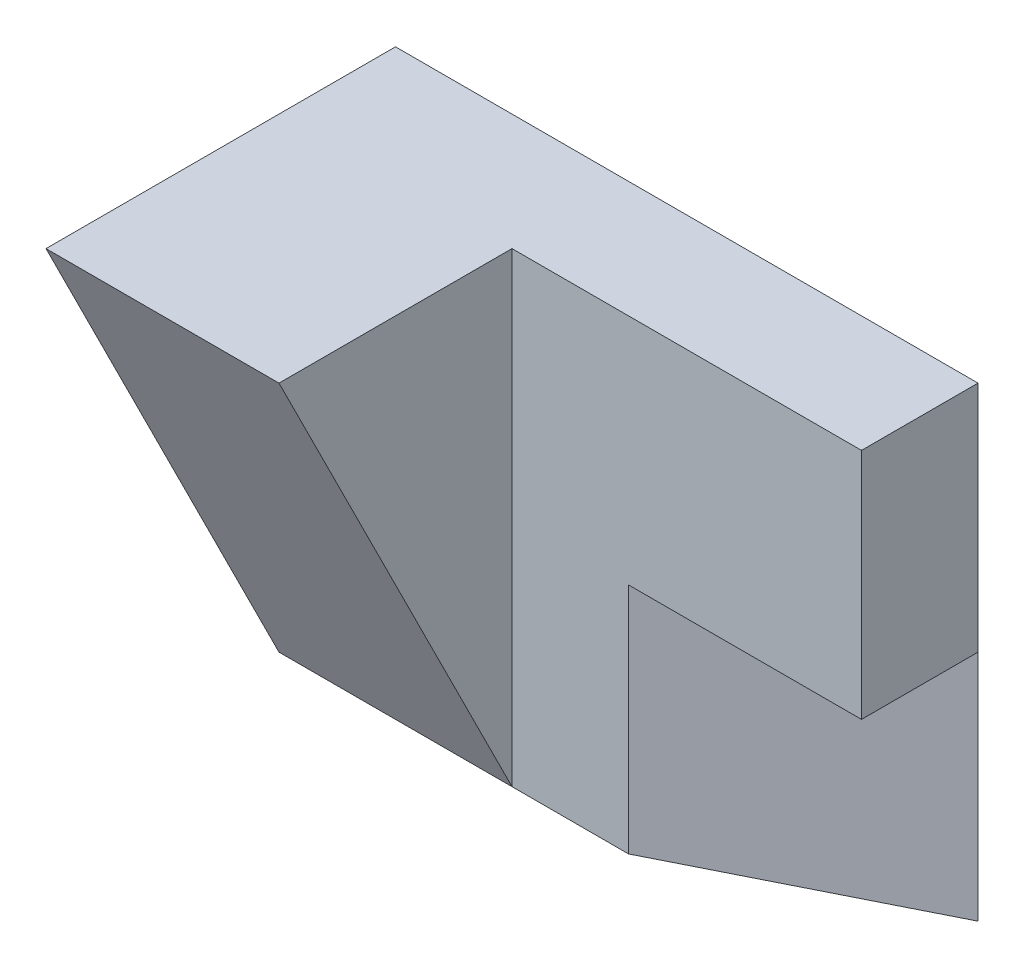
SolidWorks part; units mm, degrees
ref_plane "Front Plane" through (0, 0, 0) normal (1, 0, 0) x (0, 1, 0)
ref_plane "Top Plane" through (0, 0, 0) normal (0, 0, 1) x (0, 1, 0)
ref_plane "Right Plane" through (0, 0, 0) normal (0, 1, 0) x (-1, 0, 0)
sketch "Sketch1" plane through (0, 0, 0) normal (0, 0, 1) x (0, 1, 0)
  line L1 (0, 0) -> (40, 0)
  line L2 (0, 0) -> (0, 50)
  line L3 (0, 50) -> (40, 50)
  line L4 (40, 0) -> (40, 50)
  dimension "D1" = 40
  dimension "D2" = 50
extrude "Boss-Extrude1" add sketch "Sketch1" along normal blind 10
sketch "Sketch2" plane through (0, 0, 0) normal (0, -1, 0) x (1, 0, 0)
  line L0 (0, 10) -> (-20, 10)
  line L1 (-50, 10) -> (0, 10) construction
  line L2 (-20, 10) -> (0, 0)
  line L3 (0, 0) -> (0, 10)
  dimension "D1" = 22.3607
extrude "Cut-Extrude1" cut sketch "Sketch2" against normal blind 20
sketch "Sketch3" plane through (0, 0, 10) normal (0, 0, 1) x (1, 0, 0)
  line L0 (-50, 0) -> (-20, 0) construction
  line L1 (-50, 40) -> (-30, 40)
  line L2 (-50, 40) -> (-50, 0)
  line L3 (-50, 0) -> (-30, 0)
  line L4 (-30, 40) -> (-30, 0)
  dimension "D1" = 20
extrude "Boss-Extrude2" add sketch "Sketch3" along normal blind 20
sketch "Sketch4" plane through (-30, 0, 0) normal (1, 0, 0) x (0, 1, 0)
  line L0 (0, 10) -> (40, 30)
  line L1 (40, 30) -> (0, 30)
  line L2 (0, 30) -> (0, 10) construction
  line L3 (0, 30) -> (0, 10)
extrude "Cut-Extrude2" cut sketch "Sketch4" against normal blind 20
